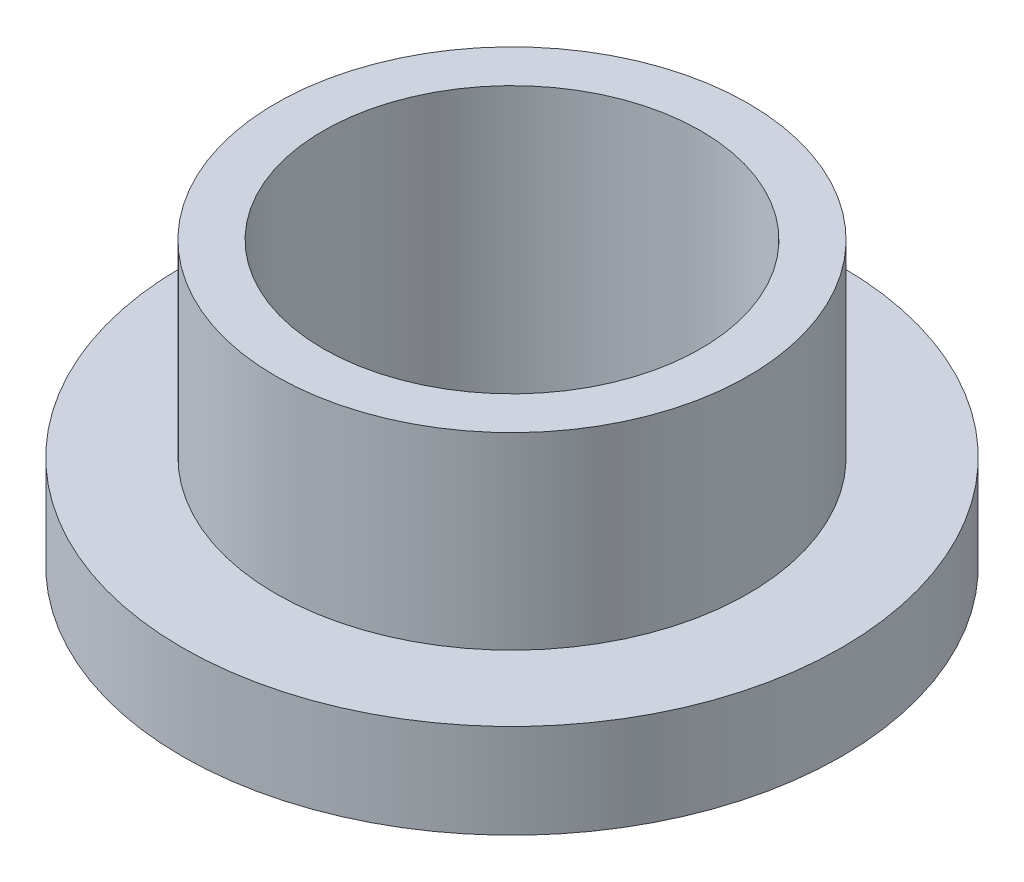
SolidWorks part; units mm, degrees
material "Brass"
ref_plane "Front" through (0, 0, 0) normal (0, 0, 1) x (1, 0, 0)
ref_plane "Top" through (0, 0, 0) normal (0, 1, 0) x (1, 0, 0)
ref_plane "Right" through (0, 0, 0) normal (1, 0, 0) x (0, 0, -1)
sketch "Sketch1" plane through (0, 0, 0) normal (0, 1, 0) x (1, 0, 0)
  circle A0 centre (0, 0) radius 6.3627
  circle A1 centre (0, 0) radius 7.9629
  circle A2 centre (0, 0) radius 11.1125
  dimension "ID" = 12.7254
  dimension "OD" = 15.9258
  dimension "FlangeOD" = 22.225
sketch "Sketch2" plane through (0, 0, 0) normal (0, 1, 0) x (1, 0, 0)
  circle A0 centre (0, 0) radius 6.3627 construction
  circle A1 centre (0, 0) radius 7.9629 construction
  circle A2 centre (0, 0) radius 6.3627
  circle A3 centre (0, 0) radius 7.9629
extrude "Boss-Extrude1" add sketch "Sketch2" along normal blind 9.525
sketch "Sketch3" plane through (0, 0, 0) normal (0, 1, 0) x (1, 0, 0)
  circle A0 centre (0, 0) radius 11.1125 construction
  circle A1 centre (0, 0) radius 7.9629 construction
  circle A2 centre (0, 0) radius 11.1125
  circle A3 centre (0, 0) radius 7.9629
extrude "Boss-Extrude2" add sketch "Sketch3" along normal blind 3.175
